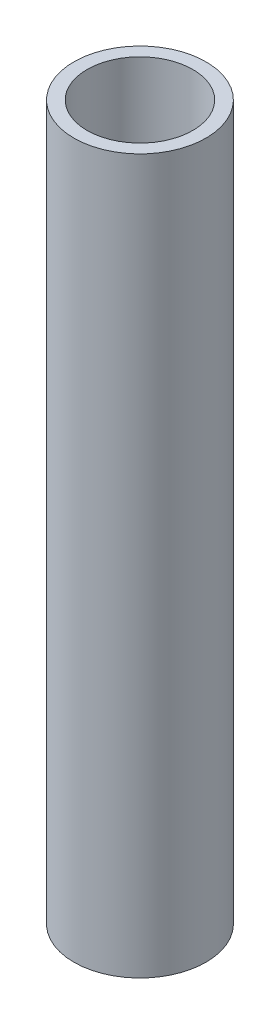
SolidWorks part; units mm, degrees
ref_plane "Alzado" through (0, 0, 0) normal (0, 0, 1) x (1, 0, 0)
ref_plane "Planta" through (0, 0, 0) normal (0, 1, 0) x (1, 0, 0)
ref_plane "Vista lateral" through (0, 0, 0) normal (1, 0, 0) x (0, 0, -1)
sketch "Croquis1" plane through (0, 0, 0) normal (0, 1, 0) x (1, 0, 0)
  circle A0 centre (0, 0) radius 5
  circle A1 centre (0, 0) radius 4
  dimension "D1" = 10
  dimension "D2" = 1
extrude "Saliente-Extruir1" add sketch "Croquis1" along normal blind 54
